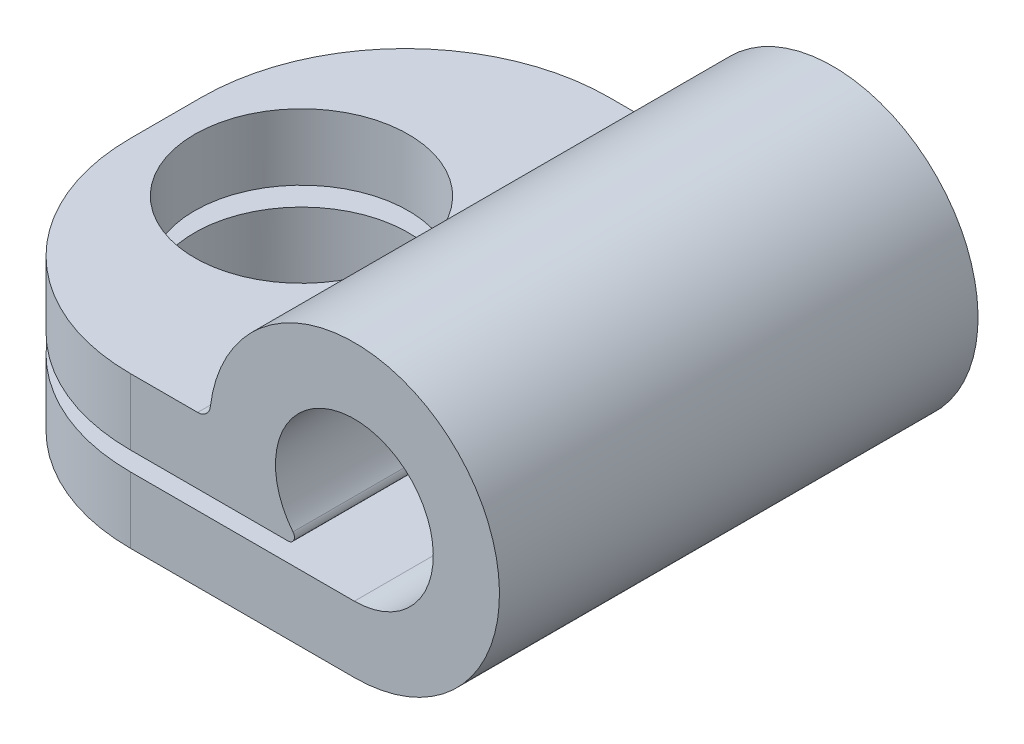
SolidWorks part; units mm, degrees
material "Nylon 6/10"
ref_plane "Front Plane" through (0, 0, 0) normal (0, 0, 1) x (1, 0, 0)
ref_plane "Top Plane" through (0, 0, 0) normal (0, 1, 0) x (1, 0, 0)
ref_plane "Right Plane" through (0, 0, 0) normal (1, 0, 0) x (0, 0, -1)
sketch "Sketch1" plane through (0, 0, 0) normal (0, 0, 1) x (1, 0, 0)
  line L0 (0, -1.55) -> (-8.4, -1.55)
  line L1 (-1.3028, -1.1778) -> (-8.4, -1.1778)
  line L2 (-3.0776, 0.1222) -> (-8.4, 0.1222)
  line L3 (0, -2.85) -> (-8.4, -2.85)
  line L4 (-8.4, 0.1222) -> (-8.4, -1.1778)
  line L5 (-8.4, -2.85) -> (-8.4, -1.55)
  arc A0 (0, -1.55) -> (-1.2056, -0.9742) centre (0, 0) ccw
  arc A1 (-1.3028, -1.1778) -> (-1.2056, -0.9742) centre (-1.3028, -1.0528) ccw
  arc A2 (0, -2.85) -> (-2.8294, 0.3422) centre (0, 0) ccw
  arc A3 (-3.0776, 0.1222) -> (-2.8294, 0.3422) centre (-3.0776, 0.3722) ccw
  point P12 (-2.8474, 0.1222)
  dimension "D1" = 3.1
  dimension "D3" = 0.125
  dimension "D5" = 5.7
  dimension "D8" = 0.25
  dimension "D2" = 8.4
  dimension "D4" = 1.3
  dimension "D6" = 5.5526
  dimension "D7" = 8.4
extrude "Boss-Extrude1" add sketch "Sketch1" along normal blind 9.4
sketch "Sketch2" plane through (0, 0.1222, 0) normal (0, 1, 0) x (1, 0, 0)
  line L0 (-3.0776, -9.4) -> (-8.4, -9.4) construction
  line L1 (-8.4, -9.4) -> (-8.4, 0) construction
  circle A0 centre (-5.7388, -4.7) radius 2.1
  dimension "D1" = 4.2
  dimension "D2" = 4.7
  dimension "D3" = 2.6612
extrude "Cut-Extrude1" cut sketch "Sketch2" against normal blind 9.4
fillet "Fillet1" radius 4 4 edges at (-8.4, -2.2, 0) (-8.4, -2.2, 9.4) (-8.4, -0.5278, 9.4) (-8.4, -0.5278, 0)
